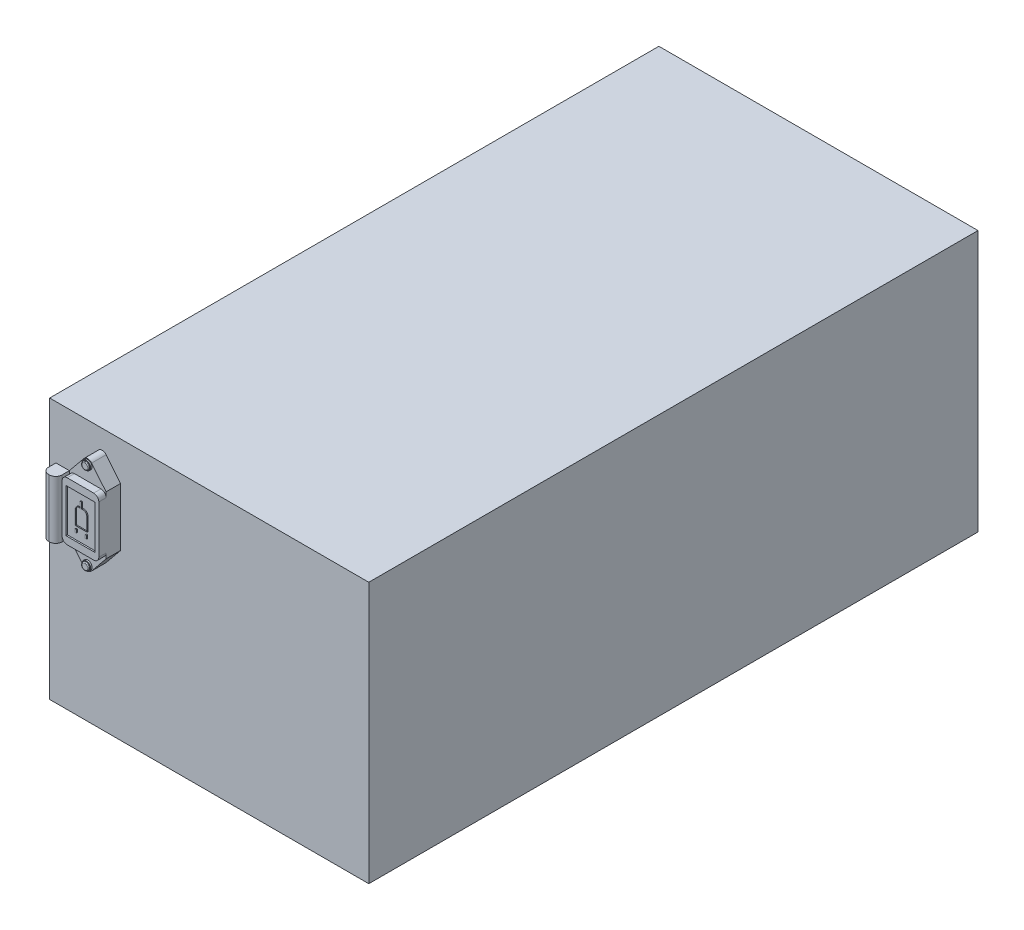
SolidWorks part; units mm, degrees
ref_plane "Front Plane" through (0, 0, 0) normal (0, 0, 1) x (1, 0, 0)
ref_plane "Top Plane" through (0, 0, 0) normal (0, 1, 0) x (1, 0, 0)
ref_plane "Right Plane" through (0, 0, 0) normal (1, 0, 0) x (0, 0, -1)
sketch "Sketch1" plane through (0, 0, 0) normal (0, 0, 1) x (1, 0, 0)
  line L1 (0, 0) -> (220, 0)
  line L2 (0, 0) -> (0, 180)
  line L3 (0, 180) -> (220, 180)
  line L4 (220, 0) -> (220, 180)
  dimension "D1" = 180
  dimension "D2" = 220
extrude "Boss-Extrude1" add sketch "Sketch1" against normal blind 420
sketch "Sketch2" plane through (0, 0, 0) normal (0, 0, 1) x (1, 0, 0)
  line L0 (23.5646, 153.3996) -> (33.5069, 165.5931)
  line L2 (23.5646, 153.3996) -> (23.5646, 113.3996)
  line L4 (48.8744, 153.3996) -> (48.8744, 113.3996)
  line L5 (38.9321, 165.5931) -> (48.8744, 153.3996)
  line L6 (23.5646, 113.3996) -> (33.5069, 101.2062)
  line L7 (38.9321, 101.2062) -> (48.8744, 113.3996)
  arc A0 (38.9321, 165.5931) -> (33.5069, 165.5931) centre (36.2195, 163.3813) ccw
  arc A1 (38.9321, 101.2062) -> (33.5069, 101.2062) centre (36.2195, 103.418) cw
  dimension "D2" = 3.5
  dimension "D3" = 3.5
  dimension "D1" = 40
extrude "Boss-Extrude2" add sketch "Sketch2" along normal blind 10
sketch "Sketch3" plane through (0, 0, 10) normal (0, 0, 1) x (1, 0, 0)
  line L1 (27.0646, 153.3996) -> (45.3744, 153.3996)
  line L2 (23.5646, 149.8996) -> (23.5646, 116.8996)
  line L3 (27.0646, 113.3996) -> (45.3744, 113.3996)
  line L4 (48.8744, 149.8996) -> (48.8744, 116.8996)
  arc A0 (48.8744, 116.8996) -> (45.3744, 113.3996) centre (45.3744, 116.8996) cw
  arc A1 (27.0646, 113.3996) -> (23.5646, 116.8996) centre (27.0646, 116.8996) cw
  arc A2 (48.8744, 149.8996) -> (45.3744, 153.3996) centre (45.3744, 149.8996) ccw
  arc A3 (27.0646, 153.3996) -> (23.5646, 149.8996) centre (27.0646, 149.8996) ccw
  point P8 (48.8744, 113.3996)
  point P15 (23.5646, 153.3996)
  dimension "D1" = 3.5
extrude "Boss-Extrude3" add sketch "Sketch3" along normal blind 5
sketch "Sketch4" plane through (0, 0, 10) normal (0, 0, 1) x (1, 0, 0)
  circle A0 centre (36.2195, 163.3813) radius 3
  circle A1 centre (36.2195, 103.418) radius 3
extrude "Boss-Extrude4" add sketch "Sketch4" along normal blind 1
sketch "Sketch5" plane through (0, 0, 11) normal (0, 0, 1) x (1, 0, 0)
  circle A0 centre (36.2195, 163.3813) radius 2.5
  circle A1 centre (36.2195, 103.418) radius 2.5
extrude "Boss-Extrude5" add sketch "Sketch5" along normal blind 1
fillet "Fillet1" radius 0.5 1 edges at (38.7195, 163.3813, 12)
fillet "Fillet2" radius 0.5 1 edges at (38.7195, 103.418, 12)
sketch "Sketch6" plane through (0, 0, 15) normal (0, 0, 1) x (1, 0, 0)
  line L0 (23.5646, 149.8996) -> (48.8744, 116.8996) construction
  line L2 (26.2195, 118.3996) -> (46.2195, 118.3996)
  line L3 (26.2195, 118.3996) -> (26.2195, 148.3996)
  line L4 (26.2195, 148.3996) -> (46.2195, 148.3996)
  line L5 (46.2195, 118.3996) -> (46.2195, 148.3996)
  line L6 (26.2195, 118.3996) -> (46.2195, 148.3996) construction
  line L7 (26.2195, 148.3996) -> (46.2195, 118.3996) construction
  arc A0 (45.3744, 113.3996) -> (48.8744, 116.8996) centre (45.3744, 116.8996) ccw construction
  point P6 (36.2195, 133.3996)
  dimension "D1" = 20
  dimension "D2" = 30
extrude "Cut-Extrude1" cut sketch "Sketch6" against normal blind 1
sketch "Sketch7" plane through (0, 0, 14) normal (0, 0, 1) x (1, 0, 0)
  line L1 (36.7562, 139.5026) -> (37.8042, 139.5026)
  line L2 (32.1348, 127.2967) -> (40.3042, 127.2967)
  line L3 (32.1348, 127.2967) -> (32.1348, 137.0026)
  line L4 (34.6348, 139.5026) -> (35.6828, 139.5026)
  line L5 (40.3042, 127.2967) -> (40.3042, 137.0026)
  line L6 (32.1348, 125.3288) -> (33.1348, 125.3288)
  line L7 (32.1348, 125.3288) -> (32.1348, 123.1853)
  line L8 (35.6828, 135.4917) -> (36.7562, 135.4917)
  line L9 (35.6828, 139.5026) -> (35.6828, 143.5134)
  line L10 (35.6828, 143.5134) -> (36.7562, 143.5134)
  line L11 (36.7562, 139.5026) -> (36.7562, 143.5134)
  line L12 (32.1348, 123.1853) -> (33.1348, 123.1853)
  line L13 (32.3848, 127.5467) -> (32.3848, 137.0026)
  line L14 (32.3848, 127.5467) -> (40.0542, 127.5467)
  line L15 (40.0542, 127.5467) -> (40.0542, 137.0026)
  line L16 (36.5062, 139.2526) -> (37.8042, 139.2526)
  line L18 (35.9328, 143.2634) -> (36.5062, 143.2634)
  line L20 (34.6348, 139.2526) -> (35.9328, 139.2526)
  line L21 (35.9328, 139.2526) -> (36.5062, 139.2526)
  line L22 (33.1348, 125.3288) -> (33.1348, 123.1853)
  line L23 (35.9328, 139.2526) -> (35.9328, 143.2634) construction
  line L24 (36.5062, 139.2526) -> (36.5062, 143.2634) construction
  line L25 (40.206, 125.3288) -> (39.206, 125.3288)
  line L26 (40.206, 125.3288) -> (40.206, 123.1853)
  line L27 (40.206, 123.1853) -> (39.206, 123.1853)
  line L28 (39.206, 125.3288) -> (39.206, 123.1853)
  arc A0 (40.3042, 137.0026) -> (37.8042, 139.5026) centre (37.8042, 137.0026) ccw
  arc A1 (34.6348, 139.5026) -> (32.1348, 137.0026) centre (34.6348, 137.0026) ccw
  arc A2 (34.6348, 139.2526) -> (32.3848, 137.0026) centre (34.6348, 137.0026) ccw
  arc A3 (40.0542, 137.0026) -> (37.8042, 139.2526) centre (37.8042, 137.0026) ccw
  point P4 (36.2195, 133.3996)
  point P9 (36.2195, 139.5026)
  dimension "D1" = 2.5
  dimension "D3" = 1
  dimension "D4" = 1
  dimension "D2" = 0.25
extrude "Boss-Extrude6" add sketch "Sketch7" along normal blind 0.7
sketch "Sketch8" plane through (0, 153.3996, 0) normal (0, 1, 0) x (1, 0, 0)
  line L1 (23.5646, -10) -> (14.3304, -10)
  line L2 (23.5646, -10) -> (23.5646, -15.1126)
  line L3 (19.3049, -19.3724) -> (18.5902, -19.3724)
  line L4 (14.3304, -10) -> (14.3304, -15.1126)
  arc A0 (23.5646, -15.1126) -> (19.3049, -19.3724) centre (19.3049, -15.1126) cw
  arc A1 (18.5902, -19.3724) -> (14.3304, -15.1126) centre (18.5902, -15.1126) cw
  dimension "D1" = 4.2597
extrude "Boss-Extrude8" add sketch "Sketch8" against normal up to vertex (40 mm away) separate body up to point (23.5646, 113.3996, 10)
